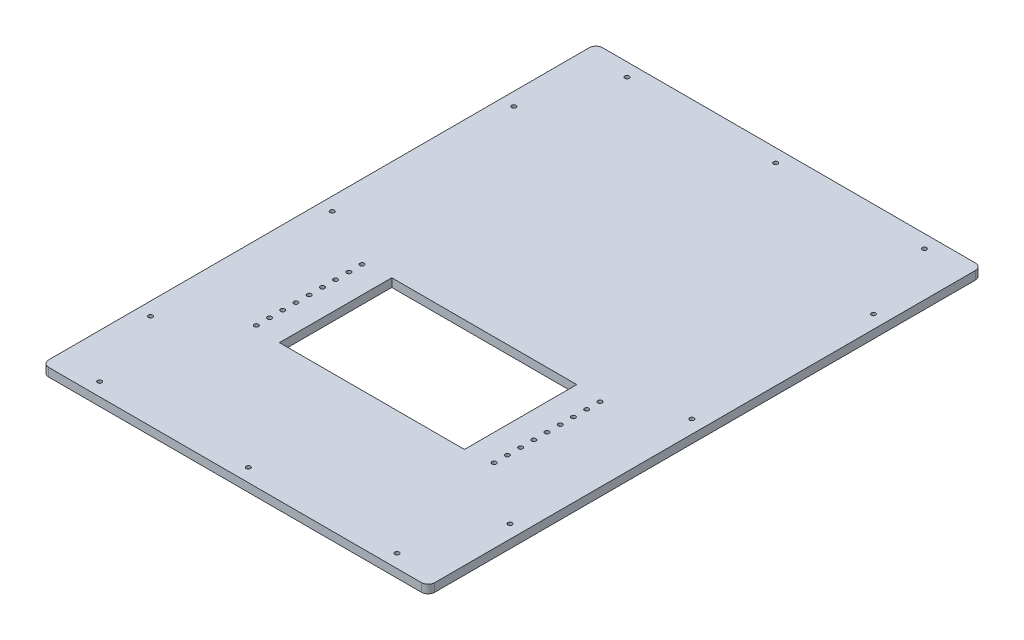
SolidWorks part; units mm, degrees
material "PC High Viscosity"
ref_plane "Front Plane" through (0, 0, 0) normal (0, 0, 1) x (1, 0, 0)
ref_plane "Top Plane" through (0, 0, 0) normal (0, 1, 0) x (1, 0, 0)
ref_plane "Right Plane" through (0, 0, 0) normal (1, 0, 0) x (0, 0, -1)
sketch "Sketch1" plane through (0, 0, 0) normal (0, 1, 0) x (1, 0, 0)
  line L1 (-292.1, 419.1) -> (292.1, 419.1)
  line L2 (-292.1, 419.1) -> (-292.1, -419.1)
  line L3 (-292.1, -419.1) -> (292.1, -419.1)
  line L4 (292.1, 419.1) -> (292.1, -419.1)
  line L5 (-292.1, 419.1) -> (292.1, -419.1) construction
  line L6 (-292.1, -419.1) -> (292.1, 419.1) construction
  point P0 (0, 0)
  dimension "D1" = 838.2
  dimension "D2" = 584.2
extrude " Lexan Boss-Extrude1" add sketch "Sketch1" along normal blind 12.7
sketch "Sketch5" plane through (0, 0, 0) normal (0, -1, 0) x (1, 0, 0)
  line L0 (-292.1, 419.1) -> (292.1, 419.1) construction
  line L1 (-140, 212) -> (140, 212)
  line L2 (-140, 212) -> (-140, 42)
  line L3 (-140, 42) -> (140, 42)
  line L4 (140, 212) -> (140, 42)
  line L5 (-140, 212) -> (140, 42) construction
  line L6 (-140, 42) -> (140, 212) construction
  line L7 (-115, 182) -> (115, 182) construction
  line L8 (-115, 182) -> (-115, 72) construction
  line L9 (-115, 72) -> (115, 72) construction
  line L10 (115, 182) -> (115, 72) construction
  line L11 (-115, 182) -> (115, 72) construction
  line L12 (-115, 72) -> (115, 182) construction
  line L13 (292.1, 419.1) -> (292.1, -419.1) construction
  point P0 (0, 127)
  point P6 (0, 127)
  dimension "D1" = 280
  dimension "D2" = 170
  dimension "D3" = 230
  dimension "D4" = 110
  dimension "D5" = 292.1
  dimension "D6" = 292.1
extrude "Housing nest hole Cut-Extrude1" cut sketch "Sketch5" against normal up to next
sketch "Sketch6" plane through (0, 0, 0) normal (0, -1, 0) x (1, 0, 0)
  line L0 (-272.1, 275) -> (-272.1, -275) construction
  line L1 (-272.1, 0) -> (0, 0) construction
  line L2 (-292.1, -419.1) -> (-292.1, 419.1) construction
  line L3 (0, 0) -> (0, 419.1) construction
  line L4 (-292.1, 419.1) -> (292.1, 419.1) construction
  line L5 (-225, 399.1) -> (225, 399.1) construction
  circle A0 centre (-272.1, 275) radius 3.25
  circle A1 centre (-272.1, 0) radius 3.25
  circle A2 centre (-272.1, -275) radius 3.25
  circle A3 centre (272.1, -275) radius 3.25
  circle A4 centre (272.1, 0) radius 3.25
  circle A5 centre (272.1, 275) radius 3.25
  circle A6 centre (-225, 399.1) radius 3.25
  circle A7 centre (0, 399.1) radius 3.25
  circle A8 centre (225, 399.1) radius 3.25
  circle A9 centre (225, -399.1) radius 3.25
  circle A10 centre (0, -399.1) radius 3.25
  circle A11 centre (-225, -399.1) radius 3.25
  dimension "D3" = 6.5
  dimension "D1" = 550
  dimension "D2" = 20
  dimension "D4" = 20
  dimension "D5" = 450
extrude "Cut-Extrude7" cut sketch "Sketch6" against normal up to next
sketch "Sketch9" plane through (0, 12.7, 0) normal (0, 1, 0) x (1, 0, 0)
  line L0 (0, -127) -> (0, 52.44) construction
  line L1 (0, -127) -> (-180, -127) construction
  line L2 (0, -127) -> (180, -127) construction
  line L3 (-140, -42) -> (140, -42) construction
  line L4 (-140, -212) -> (-140, -42) construction
  line L5 (140, -42) -> (140, -212) construction
  line L6 (140, -212) -> (-140, -212) construction
  line L7 (-140, -42) -> (140, -42) construction
  line L8 (-140, -212) -> (-140, -42) construction
  line L9 (140, -42) -> (140, -212) construction
  line L10 (140, -212) -> (-140, -212) construction
  line L11 (140, -212) -> (-140, -42) construction
  line L12 (140, -42) -> (-140, -212) construction
  circle A0 centre (-180, -127) radius 3.25
  circle A1 centre (180, -127) radius 3.25
  point P11 (0, -127)
  dimension "D1" = 6.5
  dimension "D2" = 180
extrude "Cut-Extrude6" cut sketch "Sketch9" against normal through all
pattern_linear "LPattern5" count 5 spacing 20 along (0, 0, 1) count 5 spacing 20 along (0, 0, -1) of "Cut-Extrude6"
fillet "Fillet3" radius 10 4 edges at (-292.1, 6.35, -419.1) (292.1, 6.35, -419.1) (292.1, 6.35, 419.1) (-292.1, 6.35, 419.1)
